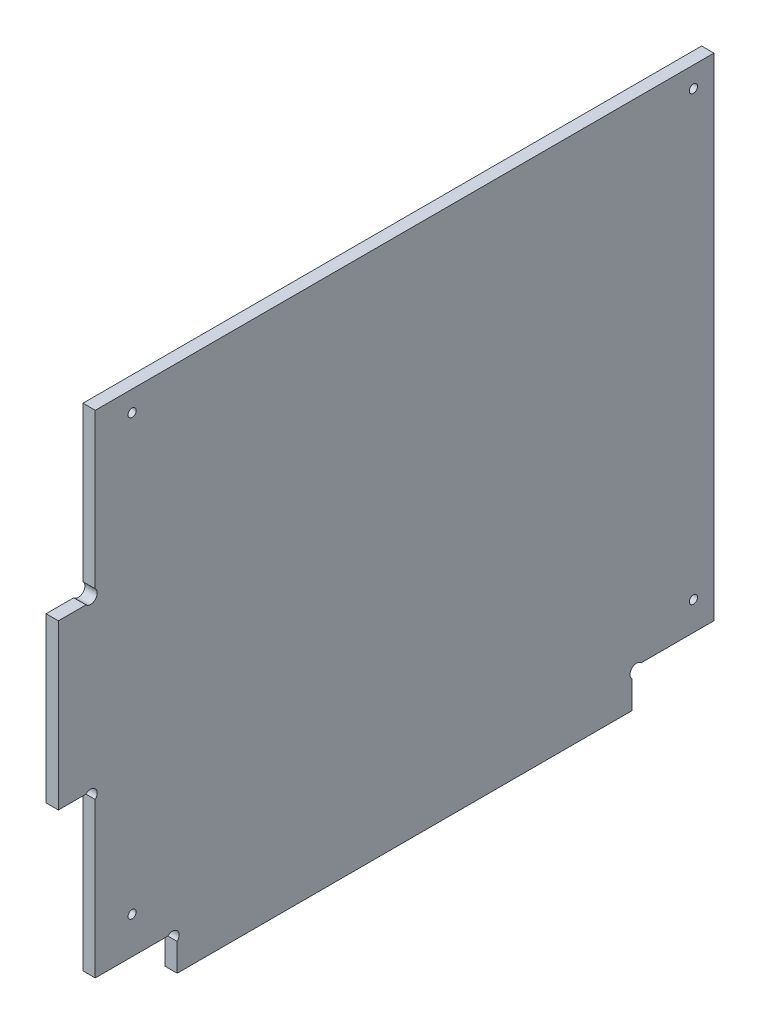
SolidWorks part; units mm, degrees
ref_plane "Plan de face" through (0, 0, 0) normal (0, 0, 1) x (1, 0, 0)
ref_plane "Plan de dessus" through (0, 0, 0) normal (0, 1, 0) x (1, 0, 0)
ref_plane "Plan de droite" through (0, 0, 0) normal (1, 0, 0) x (0, 0, -1)
sketch "Esquisse1" plane through (0, 0, 0) normal (1, 0, 0) x (0, 0, -1)
  line L11 (140, 6.7373) -> (140, 0)
  line L13 (29, 6.7373) -> (29, 0)
  line L14 (0, 49) -> (6.7373, 49)
  line L15 (0, 89) -> (6.7373, 89)
  line L16 (29, 0) -> (140, 0)
  line L17 (26.7373, 9) -> (9, 9)
  line L18 (9, 9) -> (9, 46.7373)
  line L19 (0, 49) -> (0, 89)
  line L20 (9, 91.2627) -> (9, 129)
  line L21 (9, 129) -> (160, 129)
  line L22 (160, 129) -> (160, 9)
  line L23 (160, 9) -> (142.2627, 9)
  arc A0 (142.2627, 9) -> (140, 6.7373) centre (141.1314, 7.8686) ccw
  arc A1 (9, 46.7373) -> (6.7373, 49) centre (7.8686, 47.8686) ccw
  arc A2 (26.7373, 9) -> (29, 6.7373) centre (27.8686, 7.8686) cw
  arc A3 (9, 91.2627) -> (6.7373, 89) centre (7.8686, 90.1314) cw
  dimension "D11" = 20
  dimension "D8" = 1.6
  dimension "D1" = 151
  dimension "D2" = 120
  dimension "D3" = 20
  dimension "D4" = 9
  dimension "D5" = 9
  dimension "D6" = 40
  dimension "D7" = 40
  dimension "D9" = 1.1314
  dimension "D10" = 2.2627
  dimension "D12" = 1.1314
  dimension "D13" = 2.2627
  dimension "D14" = 111
extrude "Extrusion1" add sketch "Esquisse1" along normal blind 3
sketch "Esquisse2" plane through (3, 0, 0) normal (1, 0, 0) x (0, 0, -1)
  line L0 (142.2627, 9) -> (160, 9) construction
  line L1 (160, 9) -> (160, 129) construction
  line L2 (9, 46.7373) -> (9, 9) construction
  line L3 (9, 9) -> (26.7373, 9) construction
  line L4 (160, 129) -> (9, 129) construction
  circle A0 centre (18, 124) radius 1
  circle A1 centre (155, 124) radius 1
  circle A2 centre (18, 18) radius 1
  circle A3 centre (155, 16) radius 1
  point P16 (0, 0)
  dimension "D1" = 2
  dimension "D2" = 5
  dimension "D3" = 7
  dimension "D4" = 5
  dimension "D5" = 9
  dimension "D6" = 9
extrude "Enlèv. mat.-Extru.1" cut sketch "Esquisse2" against normal through all
